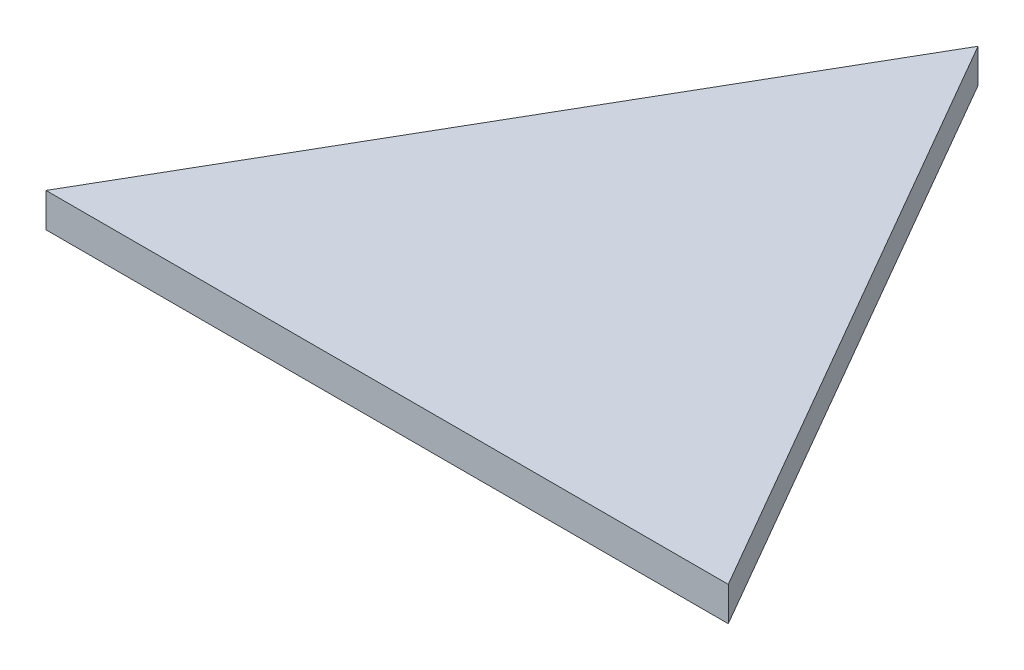
SolidWorks part; units mm, degrees
ref_plane "Front Plane" through (0, 0, 0) normal (0, 0, 1) x (1, 0, 0)
ref_plane "Top Plane" through (0, 0, 0) normal (0, 1, 0) x (1, 0, 0)
ref_plane "Right Plane" through (0, 0, 0) normal (1, 0, 0) x (0, 0, -1)
sketch "Sketch2" plane through (0, 0, 0) normal (0, 1, 0) x (1, 0, 0)
  line L0 (0, 0) -> (25.4, 0)
  line L1 (25.4, 0) -> (12.7, 21.997)
  line L2 (12.7, 21.997) -> (0, 0)
  dimension "D1" = 25.4
extrude "Boss-Extrude1" add sketch "Sketch2" along normal blind 1.27
